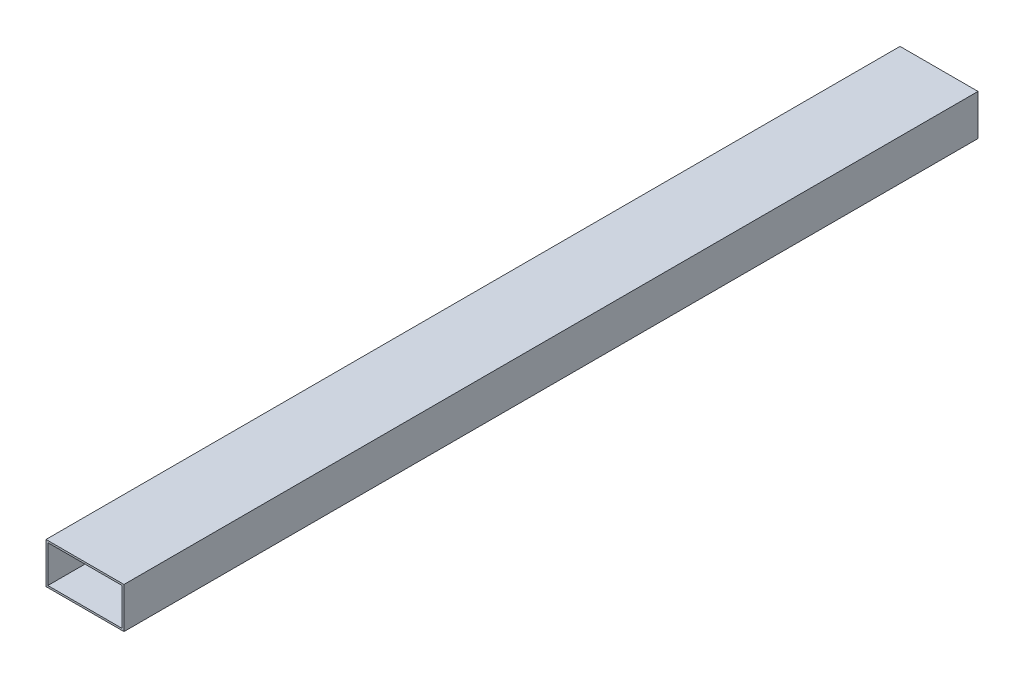
SolidWorks part; units mm, degrees
material "Pine"
ref_plane "Front Plane" through (0, 0, 0) normal (0, 0, 1) x (1, 0, 0)
ref_plane "Top Plane" through (0, 0, 0) normal (0, 1, 0) x (1, 0, 0)
ref_plane "Right Plane" through (0, 0, 0) normal (1, 0, 0) x (0, 0, -1)
sketch "Sketch1" plane through (0, 0, 0) normal (0, 0, 1) x (1, 0, 0)
  line L0 (21, 11) -> (-21, 11)
  line L1 (20, -10) -> (-20, -10)
  line L2 (20, -10) -> (20, 10)
  line L3 (20, 10) -> (-20, 10)
  line L4 (-20, -10) -> (-20, 10)
  line L5 (20, -10) -> (-20, 10) construction
  line L6 (20, 10) -> (-20, -10) construction
  line L7 (-21, -11) -> (-21, 11)
  line L8 (21, -11) -> (-21, -11)
  line L9 (21, -11) -> (21, 11)
  point P0 (0, 0)
  dimension "D1" = 40
  dimension "D2" = 20
  dimension "D3" = 1
extrude "Boss-Extrude1" add sketch "Sketch1" along normal blind 460
